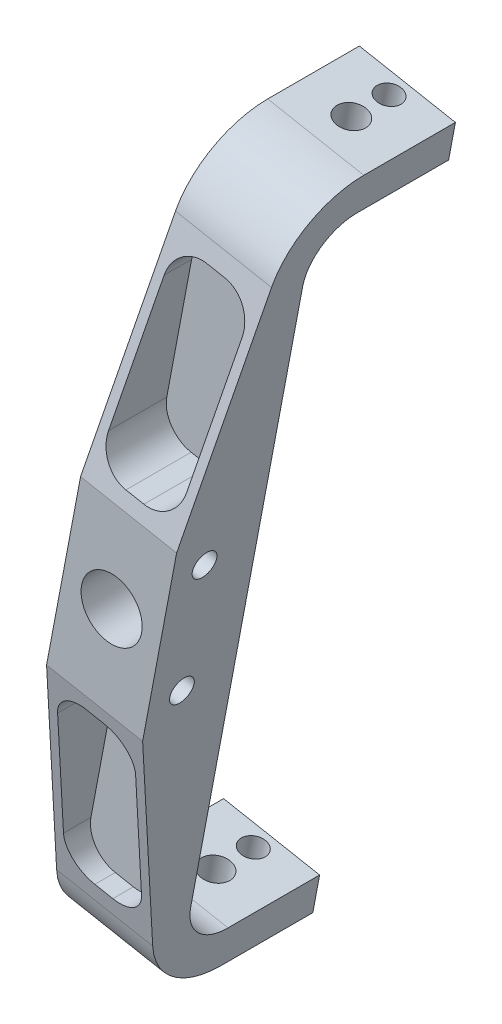
SolidWorks part; units mm, degrees
other "Markup1"
sketch "Sketch6" plane through (39.3536, 123.4271, -45) normal (0.998, 0.0328, -0.0532) x (-0.0595, 0.2351, -0.9701)
other "Markup2"
sketch "Sketch7" plane through (39.3536, 123.4271, -45) normal (0.9999, 0.0057, -0.0131) x (0.0031, -0.9818, -0.1901)
other "Markup4"
sketch "Sketch9" plane through (-39.3536, 123.4271, 27) normal (-0.9915, 0.1233, 0.0413) x (-0.1205, -0.9906, 0.0646)
other "Markup5"
sketch "Sketch12" plane through (-39.3536, 123.4271, 28.5) normal (-0.7749, 0.0474, 0.6304) x (0.632, 0.0395, 0.7739)
material "6061-T6 (SS)"
ref_plane "Front Plane" through (0, 0, 0) normal (0, 0, 1) x (1, 0, 0)
ref_plane "Top Plane" through (0, 0, 0) normal (0, 1, 0) x (1, 0, 0)
ref_plane "Right Plane" through (0, 0, 0) normal (1, 0, 0) x (0, 0, -1)
sketch "Sketch1" plane through (0, 0, 0) normal (0, 0, 1) x (1, 0, 0)
  line L0 (23.3397, 123.7002) -> (23.3397, 145.9252) construction
  line L1 (0, 0) -> (0, -276.86) construction
  line L2 (0, -276.86) -> (-52.2377, -276.86) construction
  line L3 (23.3397, 123.7002) -> (-52.2377, -276.86) construction
  line L8 (-23.3397, -123.7002) -> (-27.4603, -145.5398) construction
  line L9 (-7.6171, -126.6667) -> (39.0622, 120.7336)
  line L14 (-39.0622, -120.7336) -> (7.6171, 126.6667)
  line L17 (23.3397, 123.7002) -> (27.4603, 145.5398) construction
  line L19 (-7.6171, -126.6667) -> (-39.0622, -120.7336)
  line L20 (-23.3397, -123.7002) -> (-25.4, -134.62) construction
  line L21 (7.6171, 126.6667) -> (39.0622, 120.7336)
  line L22 (23.3397, 123.7002) -> (-23.3397, -123.7002) construction
  circle A0 centre (0, 0) radius 276.86 construction
  circle A1 centre (0, 0) radius 10
  circle A2 centre (0, 0) radius 170.5 construction
  point P4 (25.4, 134.62)
  point P6 (0, 0)
  point P10 (0, -170.5)
  point P13 (-10.5081, -129.9032)
  point P17 (0, 0)
  point P18 (41.7595, 124.248)
  point P19 (-41.8145, -123.9803)
  point P20 (10.5081, 129.9032)
  point P25 (-25.4, -134.62)
  point P31 (0, 0)
  point P32 (-23.3397, -123.7002)
  dimension "D4" = 341
  dimension "D9" = 20
  dimension "D2" = 553.72
  dimension "D3" = 22.225
  dimension "D5" = 50.8
  dimension "D6" = 32
  dimension "D7" = 52.2377
  dimension "D8" = 251.7655
  dimension "D11" = 11.1125
  dimension "D12" = 269.24
extrude "Boss-Extrude1" add sketch "Sketch1" along normal blind 28.5
sketch "Sketch2" plane through (0, 0, 0) normal (0, 0, -1) x (-1, 0, 0)
  line L0 (-36.8373, 108.9417) -> (-5.3922, 114.8748)
  line L1 (5.3922, -114.8748) -> (36.8373, -108.9417)
  line L2 (-5.3922, 114.8748) -> (-7.6171, 126.6667)
  line L3 (5.3922, -114.8748) -> (7.6171, -126.6667)
  line L4 (-7.6171, 126.6667) -> (-39.0622, 120.7336)
  line L5 (-39.0622, 120.7336) -> (7.6171, -126.6667)
  line L6 (-7.6171, 126.6667) -> (-39.0622, 120.7336)
  line L7 (39.0622, -120.7336) -> (-7.6171, 126.6667)
  line L9 (-39.0622, 120.7336) -> (-36.8373, 108.9417)
  line L11 (39.0622, -120.7336) -> (36.8373, -108.9417)
  line L14 (7.6171, -126.6667) -> (39.0622, -120.7336)
  line L15 (7.6171, -126.6667) -> (39.0622, -120.7336)
  dimension "D2" = 12
  dimension "D1" = 0
extrude "Boss-Extrude2" add sketch "Sketch2" along normal blind 45
sketch "Sketch4" plane through (-1.6562, 128.4164, 0) normal (0.1854, 0.9827, 0) x (0.9827, -0.1854, 0)
  line L0 (25.4368, -28.5) -> (25.4368, 45) construction
  line L3 (9.4368, 45) -> (41.4368, 45) construction
  line L12 (9.4368, 26.6476) -> (41.4368, 26.6476) construction
  line L13 (9.4368, -28.5) -> (9.4368, 45) construction
  line L14 (41.4368, -28.5) -> (41.4368, 45) construction
  circle A0 centre (25.4368, 26.6476) radius 4.7625
  circle A1 centre (25.4368, 39) radius 3.9688
  point P6 (25.4368, 26.6476)
  dimension "D2" = 9.525
  dimension "D3" = 7.9375
  dimension "D1" = 18.3524
  dimension "D4" = 6
extrude "Cut-Extrude1" cut sketch "Sketch4" against normal through all
fillet "Fillet3" radius 15 2 edges at (21.1148, 111.9082, 0) (-21.1148, -111.9082, 0)
sketch "Sketch10" plane through (-16.0243, 1.3676, 0) normal (0.9827, -0.1854, 0) x (0, 0, -1)
  line L0 (-28.5, 31.6271) -> (-11.3167, 106.5459)
  line L1 (-28.5, 31.6271) -> (-46.9139, 31.6271)
  line L2 (-46.9139, 31.6271) -> (-43.5283, 140.3502)
  line L3 (-43.5283, 140.3502) -> (15, 127.5099)
  line L4 (0, 1.6271) -> (-52.8517, 1.6271) construction
  line L5 (-28.5, 127.5099) -> (45, 127.5099) construction
  line L6 (-28.5, -124.2556) -> (-28.5, 127.5099) construction
  line L7 (-43.5283, -137.0959) -> (15, -124.2556)
  line L8 (-46.9139, -28.3729) -> (-43.5283, -137.0959)
  line L9 (-28.5, -28.3729) -> (-46.9139, -28.3729)
  line L10 (-28.5, -28.3729) -> (-11.3167, -103.2916)
  arc A0 (15, 115.5099) -> (0, 100.5099) centre (15, 100.5099) ccw construction
  arc A1 (15, 115.5099) -> (0, 100.5099) centre (15, 100.5099) ccw construction
  arc A2 (15, 127.5099) -> (-11.3167, 106.5459) centre (15, 100.5099) ccw
  arc A3 (15, -112.2556) -> (0, -97.2556) centre (15, -97.2556) cw construction
  arc A4 (15, -124.2556) -> (-11.3167, -103.2916) centre (15, -97.2556) cw
  circle A5 centre (-17.5, 21.6271) radius 4
  circle A6 centre (-17.5, -18.3729) radius 4
  point P14 (15, 127.5099)
  point P29 (15, -124.2556)
  dimension "D1" = 0
  dimension "D2" = 8
  dimension "D3" = 30
  dimension "D4" = 20
  dimension "D5" = 17.5
extrude "Cut-Extrude2" cut sketch "Sketch10" against normal through all both and the other way through all
sketch "Sketch11" plane through (0, 0, 28.5) normal (0, 0, 1) x (1, 0, 0)
  line L1 (0, 0) -> (75.6649, -14.2764) construction
  line L2 (35.1753, 100.1331) -> (21.2848, 26.5133) construction
  line L3 (35.1753, 100.1331) -> (21.2848, 26.5133) construction
  line L7 (3.5413, 34.9494) -> (9.4373, 33.8369)
  line L12 (-10.1604, 32.4464) -> (3.7302, 106.0662) construction
  line L13 (-10.1604, 32.4464) -> (3.7302, 106.0662) construction
  line L15 (21.118, 41.8095) -> (29.2542, 84.9314)
  line L26 (-4.4312, 46.6301) -> (3.705, 89.752)
  line L27 (2.6111, 100.1348) -> (34.0562, 94.2018) construction
  line L39 (15.3857, 97.7245) -> (21.2816, 96.6121)
  line L40 (-21.2848, -26.5133) -> (-35.1753, -100.1331) construction
  line L41 (-3.7302, -106.0662) -> (10.1604, -32.4464) construction
  line L42 (-21.2816, -96.6121) -> (-15.3857, -97.7245)
  line L43 (-21.118, -41.8095) -> (-29.2542, -84.9314)
  line L44 (4.4312, -46.6301) -> (-3.705, -89.752)
  line L45 (-9.4373, -33.8369) -> (-3.5413, -34.9494)
  arc A0 (9.4373, 33.8369) -> (21.118, 41.8095) centre (11.2913, 43.6636) ccw
  arc A1 (3.5413, 34.9494) -> (-4.4312, 46.6301) centre (5.3954, 44.776) cw
  arc A2 (15.3857, 97.7245) -> (3.705, 89.752) centre (13.5316, 87.8979) ccw
  arc A3 (29.2542, 84.9314) -> (21.2816, 96.6121) centre (19.4275, 86.7855) ccw
  arc A4 (-3.705, -89.752) -> (-15.3857, -97.7245) centre (-13.5316, -87.8979) cw
  arc A5 (-21.2816, -96.6121) -> (-29.2542, -84.9314) centre (-19.4275, -86.7855) cw
  arc A6 (-9.4373, -33.8369) -> (-21.118, -41.8095) centre (-11.2913, -43.6636) ccw
  arc A7 (-3.5413, -34.9494) -> (4.4312, -46.6301) centre (-5.3954, -44.776) cw
  point P12 (-3.4131, 31.3285)
  point P15 (10.5274, 99.16)
  point P16 (29.4323, 95.2747)
  point P17 (15.4917, 27.4432)
  point P18 (27.5728, 26.3797)
  point P19 (-17.6556, 26.3797)
  dimension "D4" = 10
  dimension "D2" = 6
  dimension "D1" = 35
  dimension "D3" = 6
extrude "Cut-Extrude4" cut sketch "Sketch11" against normal offset from surface (22.5 mm away) 6 up to face at (10, 0, 0)
